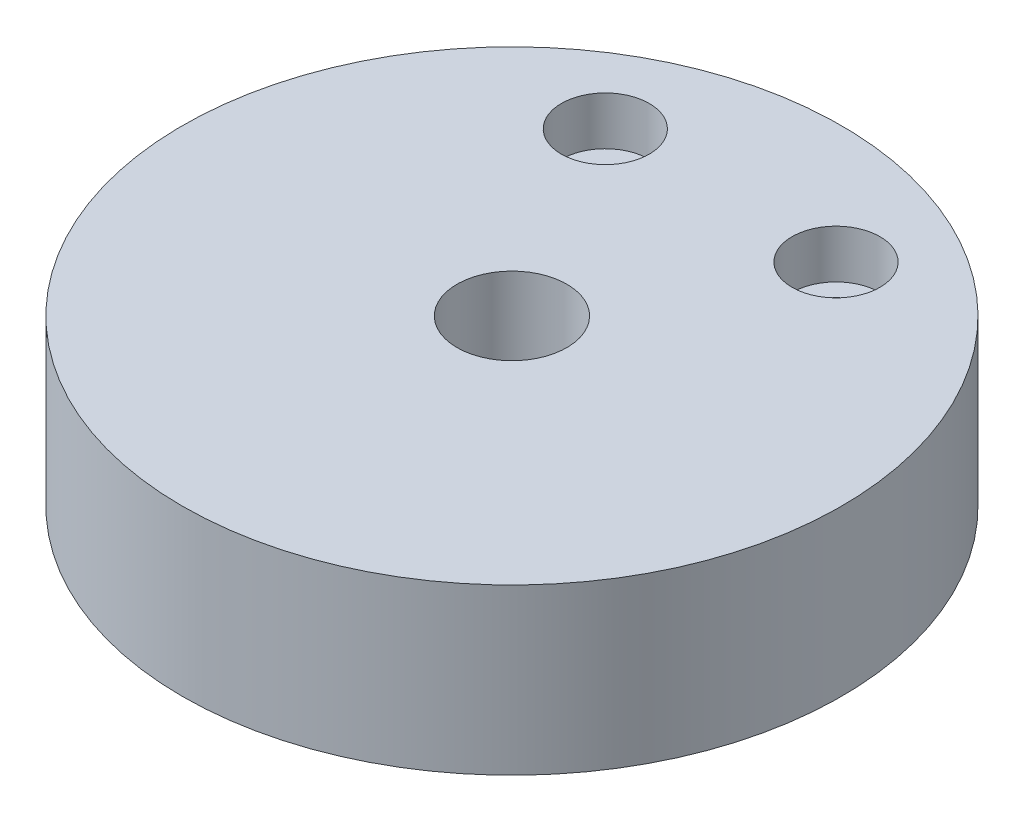
SolidWorks part; units mm, degrees
ref_plane "Front Plane" through (0, 0, 0) normal (0, 0, 1) x (1, 0, 0)
ref_plane "Top Plane" through (0, 0, 0) normal (0, 1, 0) x (1, 0, 0)
ref_plane "Right Plane" through (0, 0, 0) normal (1, 0, 0) x (0, 0, -1)
sketch "Sketch9" plane through (0, 0, 0) normal (0, 1, 0) x (1, 0, 0)
  line L0 (93.0887, 141.0799) -> (115.5887, 141.0799) construction
  circle A0 centre (121.7221, 83.9358) radius 6.8074
  circle A1 centre (113.5011, 102.9358) radius 1.5056
  circle A2 centre (132.5011, 101.4333) radius 1.4477
  dimension "D2" = 19
  dimension "D3" = 19
  dimension "D1" = 22.5
sketch "Sketch1" plane through (0, 0, 0) normal (0, 1, 0) x (1, 0, 0)
  circle A0 centre (121.7221, 83.9358) radius 30
  point P6 (121.7221, 83.9358)
  dimension "D3" = 60
extrude "Boss-Extrude1" add sketch "Sketch1" along normal blind 15
sketch "Sketch10" plane through (0, 15, 0) normal (0, 1, 0) x (1, 0, 0)
  circle A0 centre (121.7221, 83.9358) radius 5
  dimension "D1" = 10
extrude "Cut-Extrude2" cut sketch "Sketch10" against normal blind 15
sketch "Sketch11" plane through (0, 15, 0) normal (0, 1, 0) x (1, 0, 0)
  line L0 (91.7221, 83.9358) -> (151.7221, 83.9358) construction
  line L1 (121.7221, 113.9358) -> (121.7221, 53.9358) construction
  circle A0 centre (121.7221, 83.9358) radius 30 construction
  point P7 (111.2221, 102.9358)
  point P8 (132.2221, 102.9358)
  dimension "D1" = 19
  dimension "D2" = 10.5
hole_wizard "CBORE for M4 Hex Socket Head Cap Screw3" positions "3DSketch4" profile "Sketch12" counterbore size "M4" standard "ISO" end condition up to next
sketch3d "3DSketch4"
  point P0 (132.2221, 15, -102.9358)
  point P3 (111.2221, 15, -102.9358)
sketch "Sketch12" plane through (132.2221, 15, -102.9358) normal (1, 0, 0) x (0, 0, 1)
  line L0 (0, 0) -> (0, 15)
  line L1 (0, 15) -> (2.25, 15)
  line L3 (2.25, 15) -> (2.25, 4.4)
  line L4 (2.25, 4.4) -> (4, 4.4)
  line L5 (4, 4.4) -> (4, 0)
  line L7 (4, 0) -> (0, 0)
  line L11 (0, -6.35) -> (0, 107.95) construction
  dimension "Thru Hole Dia." = 4.5
  dimension "Thru Hole Depth" = 15
  dimension "C'Bore Dia." = 8
  dimension "C'Bore Depth" = 4.4
